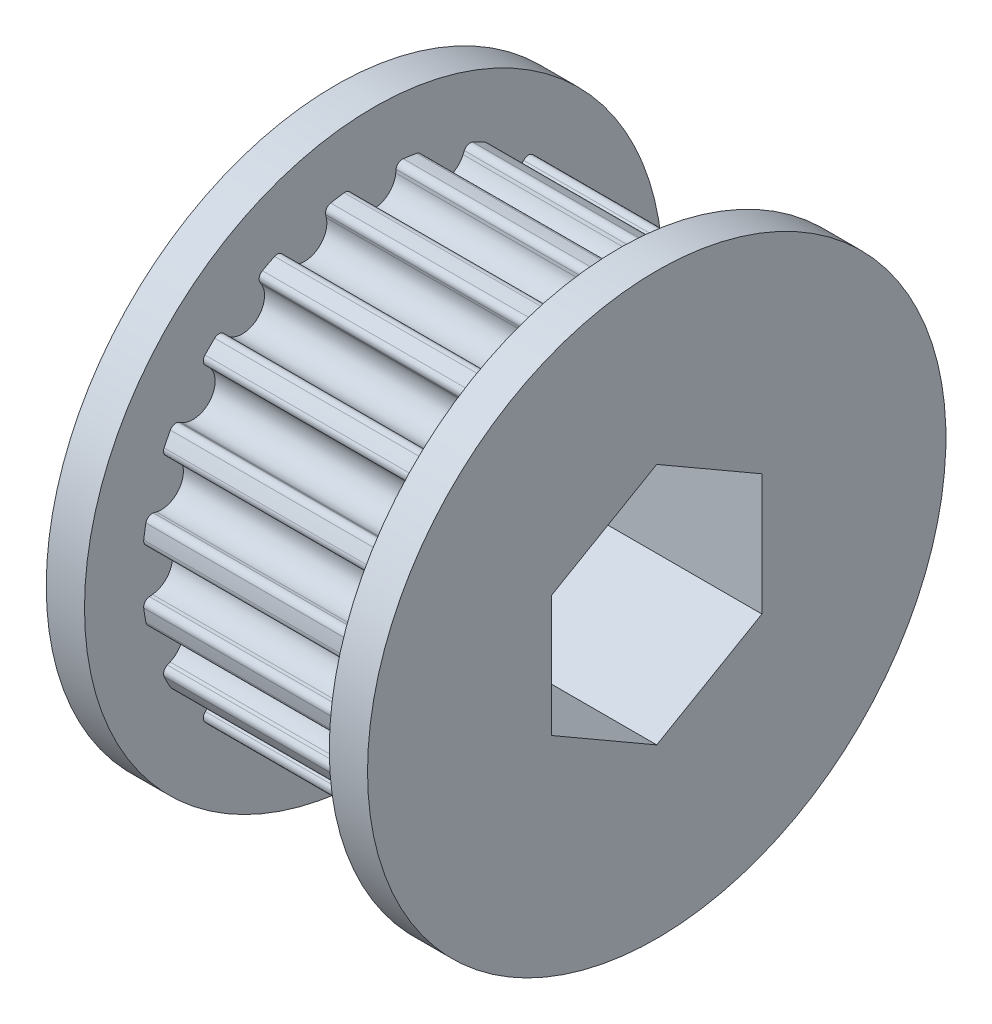
SolidWorks part; units mm, degrees
ref_plane "Front Plane" through (0, 0, 0) normal (0, 0, 1) x (1, 0, 0)
ref_plane "Top Plane" through (0, 0, 0) normal (0, 1, 0) x (1, 0, 0)
ref_plane "Right Plane" through (0, 0, 0) normal (1, 0, 0) x (0, 0, -1)
ref_plane "Plane1" through (0, 0, 0) normal (0, 0, -1) x (-1, 0, 0)
sketch "Sketch1" plane through (0, 0, 0) normal (0, 0, -1) x (-1, 0, 0)
  line L0 (-18.796, 19.2055) -> (-18.796, 0)
  line L1 (-18.796, 0) -> (-16.256, 0)
  line L2 (-16.256, 0) -> (-16.256, 19.2055)
  line L3 (-16.256, 19.2055) -> (-18.796, 19.2055)
  line L4 (-18.796, 0) -> (-16.256, 0) construction
revolve "Revolve1" add sketch "Sketch1" angle 360 about L4
sketch "Sketch2" plane through (16.256, 0, 0) normal (-1, 0, 0) x (0, 0, 1)
  line L0 (-14.6904, 1.4659) -> (-15.3194, 1.5287)
  line L1 (-15.042, 3.2801) -> (-14.4244, 3.1454)
  line L2 (-13.5184, 5.9337) -> (-14.0972, 6.1878)
  line L3 (-13.2922, 7.7678) -> (-12.7464, 7.4488)
  line L4 (-11.0231, 9.8207) -> (-11.4951, 10.2412)
  line L5 (-10.2412, 11.4951) -> (-9.8207, 11.0231)
  line L6 (-7.4488, 12.7464) -> (-7.7678, 13.2922)
  line L7 (-6.1878, 14.0972) -> (-5.9337, 13.5184)
  line L8 (-3.1454, 14.4244) -> (-3.2801, 15.042)
  line L9 (-1.5287, 15.3194) -> (-1.4659, 14.6904)
  line L10 (1.4659, 14.6904) -> (1.5287, 15.3194)
  line L11 (3.2801, 15.042) -> (3.1454, 14.4244)
  line L12 (5.9337, 13.5184) -> (6.1878, 14.0972)
  line L13 (7.7678, 13.2922) -> (7.4488, 12.7464)
  line L14 (9.8207, 11.0231) -> (10.2412, 11.4951)
  line L15 (11.4951, 10.2412) -> (11.0231, 9.8207)
  line L16 (12.7464, 7.4488) -> (13.2922, 7.7678)
  line L17 (14.0972, 6.1878) -> (13.5184, 5.9337)
  line L18 (14.4244, 3.1454) -> (15.042, 3.2801)
  line L19 (15.3194, 1.5287) -> (14.6904, 1.4659)
  line L20 (14.6904, -1.4659) -> (15.3194, -1.5287)
  line L21 (15.042, -3.2801) -> (14.4244, -3.1454)
  line L22 (13.5184, -5.9337) -> (14.0972, -6.1878)
  line L23 (13.2922, -7.7678) -> (12.7464, -7.4488)
  line L24 (11.0231, -9.8207) -> (11.4951, -10.2412)
  line L25 (10.2412, -11.4951) -> (9.8207, -11.0231)
  line L26 (7.4488, -12.7464) -> (7.7678, -13.2922)
  line L27 (6.1878, -14.0972) -> (5.9337, -13.5184)
  line L28 (3.1454, -14.4244) -> (3.2801, -15.042)
  line L29 (1.5287, -15.3194) -> (1.4659, -14.6904)
  line L30 (-1.4659, -14.6904) -> (-1.5287, -15.3194)
  line L31 (-3.2801, -15.042) -> (-3.1454, -14.4244)
  line L32 (-5.9337, -13.5184) -> (-6.1878, -14.0972)
  line L33 (-7.7678, -13.2922) -> (-7.4488, -12.7464)
  line L34 (-9.8207, -11.0231) -> (-10.2412, -11.4951)
  line L35 (-11.4951, -10.2412) -> (-11.0231, -9.8207)
  line L36 (-12.7464, -7.4488) -> (-13.2922, -7.7678)
  line L37 (-14.0972, -6.1878) -> (-13.5184, -5.9337)
  line L38 (-14.4244, -3.1454) -> (-15.042, -3.2801)
  line L39 (-15.3194, -1.5287) -> (-14.6904, -1.4659)
  arc A0 (-15.3194, 1.5287) -> (-15.042, 3.2801) centre (0, 0) cw
  arc A1 (-14.4244, 3.1454) -> (-13.5184, 5.9337) centre (-14.1105, 4.5848) ccw
  arc A2 (-14.0972, 6.1878) -> (-13.2922, 7.7678) centre (0, 0) cw
  arc A3 (-12.7464, 7.4488) -> (-11.0231, 9.8207) centre (-12.0031, 8.7208) ccw
  arc A4 (-11.4951, 10.2412) -> (-10.2412, 11.4951) centre (0, 0) cw
  arc A5 (-9.8207, 11.0231) -> (-7.4488, 12.7464) centre (-8.7208, 12.0031) ccw
  arc A6 (-7.7678, 13.2922) -> (-6.1878, 14.0972) centre (0, 0) cw
  arc A7 (-5.9337, 13.5184) -> (-3.1454, 14.4244) centre (-4.5848, 14.1105) ccw
  arc A8 (-3.2801, 15.042) -> (-1.5287, 15.3194) centre (0, 0) cw
  arc A9 (-1.4659, 14.6904) -> (1.4659, 14.6904) centre (0, 14.8367) ccw
  arc A10 (1.5287, 15.3194) -> (3.2801, 15.042) centre (0, 0) cw
  arc A11 (3.1454, 14.4244) -> (5.9337, 13.5184) centre (4.5848, 14.1105) ccw
  arc A12 (6.1878, 14.0972) -> (7.7678, 13.2922) centre (0, 0) cw
  arc A13 (7.4488, 12.7464) -> (9.8207, 11.0231) centre (8.7208, 12.0031) ccw
  arc A14 (10.2412, 11.4951) -> (11.4951, 10.2412) centre (0, 0) cw
  arc A15 (11.0231, 9.8207) -> (12.7464, 7.4488) centre (12.0031, 8.7208) ccw
  arc A16 (13.2922, 7.7678) -> (14.0972, 6.1878) centre (0, 0) cw
  arc A17 (13.5184, 5.9337) -> (14.4244, 3.1454) centre (14.1105, 4.5848) ccw
  arc A18 (15.042, 3.2801) -> (15.3194, 1.5287) centre (0, 0) cw
  arc A19 (14.6904, 1.4659) -> (14.6904, -1.4659) centre (14.8367, 0) ccw
  arc A20 (15.3194, -1.5287) -> (15.042, -3.2801) centre (0, 0) cw
  arc A21 (14.4244, -3.1454) -> (13.5184, -5.9337) centre (14.1105, -4.5848) ccw
  arc A22 (14.0972, -6.1878) -> (13.2922, -7.7678) centre (0, 0) cw
  arc A23 (12.7464, -7.4488) -> (11.0231, -9.8207) centre (12.0031, -8.7208) ccw
  arc A24 (11.4951, -10.2412) -> (10.2412, -11.4951) centre (0, 0) cw
  arc A25 (9.8207, -11.0231) -> (7.4488, -12.7464) centre (8.7208, -12.0031) ccw
  arc A26 (7.7678, -13.2922) -> (6.1878, -14.0972) centre (0, 0) cw
  arc A27 (5.9337, -13.5184) -> (3.1454, -14.4244) centre (4.5848, -14.1105) ccw
  arc A28 (3.2801, -15.042) -> (1.5287, -15.3194) centre (0, 0) cw
  arc A29 (1.4659, -14.6904) -> (-1.4659, -14.6904) centre (0, -14.8367) ccw
  arc A30 (-1.5287, -15.3194) -> (-3.2801, -15.042) centre (0, 0) cw
  arc A31 (-3.1454, -14.4244) -> (-5.9337, -13.5184) centre (-4.5848, -14.1105) ccw
  arc A32 (-6.1878, -14.0972) -> (-7.7678, -13.2922) centre (0, 0) cw
  arc A33 (-7.4488, -12.7464) -> (-9.8207, -11.0231) centre (-8.7208, -12.0031) ccw
  arc A34 (-10.2412, -11.4951) -> (-11.4951, -10.2412) centre (0, 0) cw
  arc A35 (-11.0231, -9.8207) -> (-12.7464, -7.4488) centre (-12.0031, -8.7208) ccw
  arc A36 (-13.2922, -7.7678) -> (-14.0972, -6.1878) centre (0, 0) cw
  arc A37 (-13.5184, -5.9337) -> (-14.4244, -3.1454) centre (-14.1105, -4.5848) ccw
  arc A38 (-15.042, -3.2801) -> (-15.3194, -1.5287) centre (0, 0) cw
  arc A39 (-14.6904, -1.4659) -> (-14.6904, 1.4659) centre (-14.8367, 0) ccw
extrude "Boss-Extrude1" add sketch "Sketch2" along normal blind 16.256
sketch "Sketch3" plane through (0, 0, 0) normal (1, 0, 0) x (0, 0, -1)
  circle A0 centre (0, 0) radius 19.2055
extrude "Boss-Extrude2" add sketch "Sketch3" against normal blind 2.54
sketch "Sketch4" plane through (-2.54, 0, 0) normal (-1, 0, 0) x (0, 0, 1)
  line L0 (0, 8.0656) -> (-6.985, 4.0328)
  line L1 (-6.985, 4.0328) -> (-6.985, -4.0328)
  line L2 (-6.985, -4.0328) -> (0, -8.0656)
  line L3 (0, -8.0656) -> (6.985, -4.0328)
  line L4 (6.985, -4.0328) -> (6.985, 4.0328)
  line L5 (6.985, 4.0328) -> (0, 8.0656)
extrude "Cut-Extrude1" cut sketch "Sketch4" against normal through all
fillet "Fillet1" radius 0.42 40 edges at (8.128, 14.0972, 6.1878) (8.128, 10.2412, -11.4951) (8.128, 1.5287, 15.3194) (8.128, -6.1878, 14.0972) (8.128, 15.042, -3.2801) (8.128, -7.7678, 13.2922) (8.128, 7.7678, 13.2922) (8.128, -10.2412, 11.4951) (8.128, 6.1878, -14.0972) (8.128, -11.4951, 10.2412) (8.128, 13.2922, -7.7678) (8.128, -13.2922, 7.7678) (8.128, 15.3194, 1.5287) (8.128, -14.0972, 6.1878) (8.128, 11.4951, 10.2412) (8.128, -15.042, 3.2801) (8.128, 3.2801, 15.042) (8.128, -15.3194, 1.5287) (8.128, 3.2801, -15.042) (8.128, -15.3194, -1.5287) (8.128, 7.7678, -13.2922) (8.128, -15.042, -3.2801) (8.128, 11.4951, -10.2412) (8.128, -14.0972, -6.1878) (8.128, 14.0972, -6.1878) (8.128, -13.2922, -7.7678) (8.128, 15.3194, -1.5287) (8.128, -11.4951, -10.2412) (8.128, 15.042, 3.2801) (8.128, -10.2412, -11.4951) (8.128, 13.2922, 7.7678) (8.128, -7.7678, -13.2922) (8.128, 10.2412, 11.4951) (8.128, -6.1878, -14.0972) (8.128, 6.1878, 14.0972) (8.128, -3.2801, -15.042) (8.128, -1.5287, 15.3194) (8.128, -1.5287, -15.3194) (8.128, -3.2801, 15.042) (8.128, 1.5287, -15.3194)
